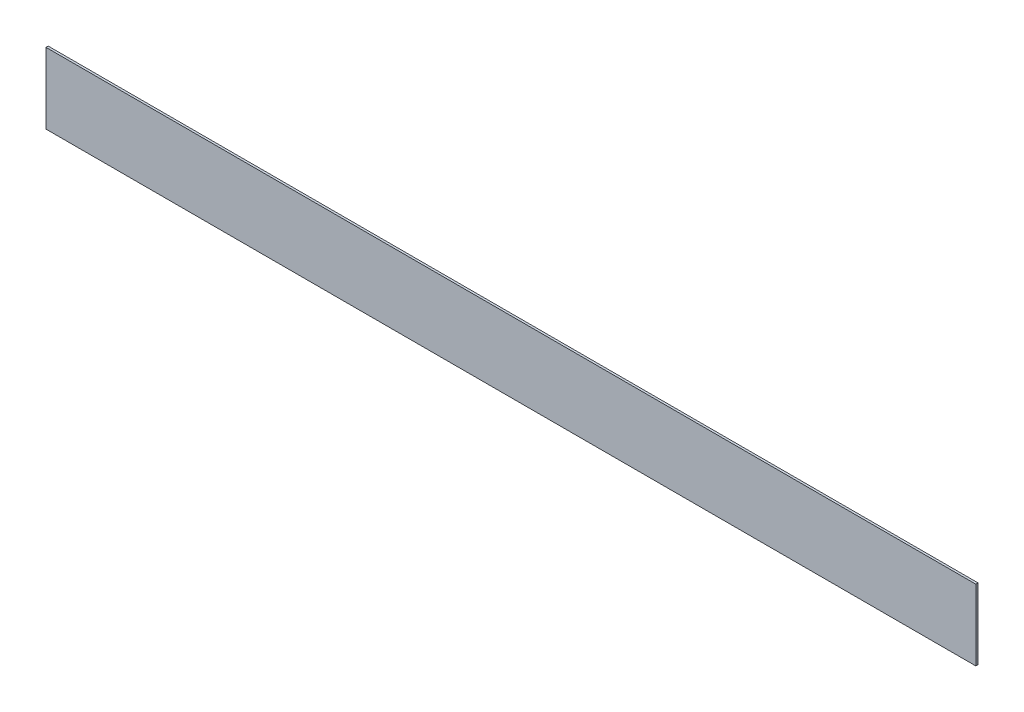
SolidWorks part; units mm, degrees
ref_plane "前视基准面" through (0, 0, 0) normal (0, 0, 1) x (1, 0, 0)
ref_plane "上视基准面" through (0, 0, 0) normal (0, 1, 0) x (1, 0, 0)
ref_plane "右视基准面" through (0, 0, 0) normal (1, 0, 0) x (0, 0, -1)
sketch "草图1" plane through (0, 0, 0) normal (0, 0, 1) x (1, 0, 0)
  line L1 (-21, -1.6) -> (21, -1.6)
  line L2 (-21, -1.6) -> (-21, 1.6)
  line L3 (-21, 1.6) -> (21, 1.6)
  line L4 (21, -1.6) -> (21, 1.6)
  line L5 (-21, -1.6) -> (21, 1.6) construction
  line L6 (-21, 1.6) -> (21, -1.6) construction
  point P0 (0, 0)
  dimension "D1" = 42
  dimension "D2" = 3.2
extrude "凸台-拉伸1" add sketch "草图1" along normal blind 0.1
